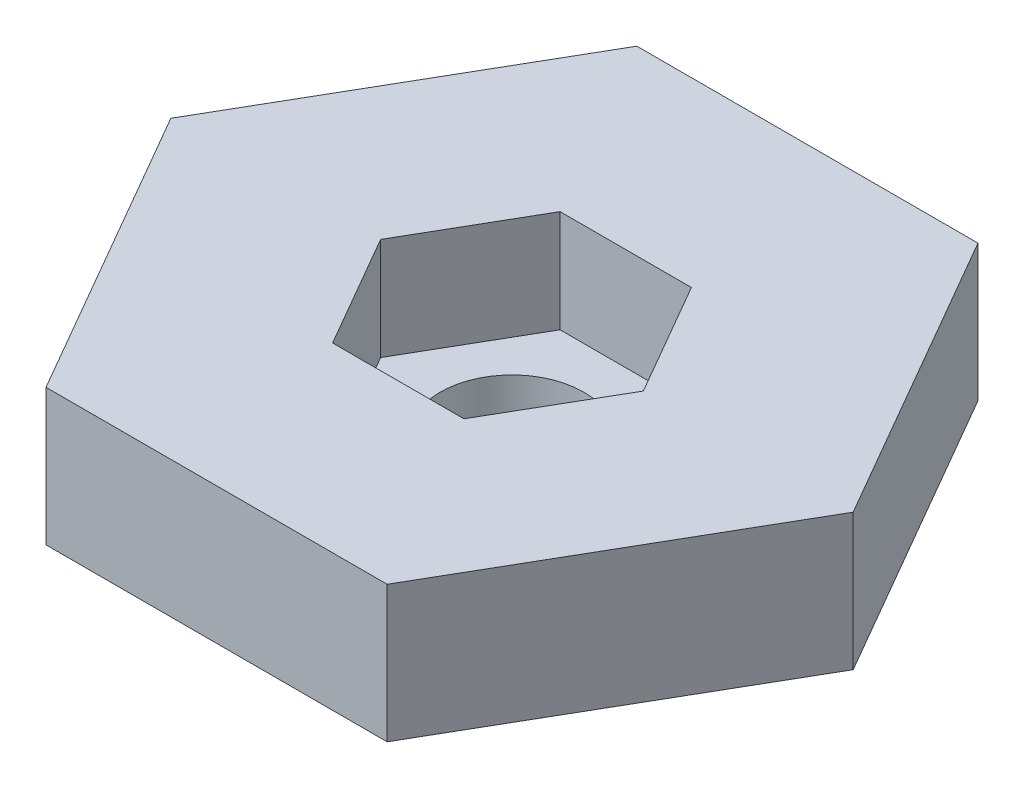
SolidWorks part; units mm, degrees
ref_plane "Спереди" through (0, 0, 0) normal (0, 0, 1) x (1, 0, 0)
ref_plane "Сверху" through (0, 0, 0) normal (0, 1, 0) x (1, 0, 0)
ref_plane "Справа" through (0, 0, 0) normal (1, 0, 0) x (0, 0, -1)
sketch "Sketch1" plane through (0, 0, 0) normal (0, 1, 0) x (1, 0, 0)
  line L1 (-10, 17.3205) -> (-20, 0)
  line L2 (-20, 0) -> (-10, -17.3205)
  line L3 (-10, -17.3205) -> (10, -17.3205)
  line L4 (10, -17.3205) -> (20, 0)
  line L5 (20, 0) -> (10, 17.3205)
  line L6 (10, 17.3205) -> (-10, 17.3205)
  line L7 (-3.85, 6.6684) -> (-7.7, 0)
  line L8 (-7.7, 0) -> (-3.85, -6.6684)
  line L9 (-3.85, -6.6684) -> (3.85, -6.6684)
  line L10 (3.85, -6.6684) -> (7.7, 0)
  line L11 (7.7, 0) -> (3.85, 6.6684)
  line L12 (3.85, 6.6684) -> (-3.85, 6.6684)
  circle A0 centre (0, 0) radius 20 construction
  circle A1 centre (0, 0) radius 7.7 construction
  dimension "D1" = 40
  dimension "D2" = 15.4
extrude "Boss-Extrude1" add sketch "Sketch1" along normal blind 6
sketch "Sketch2" plane through (0, 0, 0) normal (0, -1, 0) x (1, 0, 0)
  line L0 (20, 0) -> (10, -17.3205)
  line L1 (10, -17.3205) -> (-10, -17.3205)
  line L2 (-10, -17.3205) -> (-20, 0)
  line L3 (-20, 0) -> (-10, 17.3205)
  line L4 (-20, 0) -> (-10, 17.3205) construction
  line L5 (-10, 17.3205) -> (10, 17.3205) construction
  line L6 (-10, 17.3205) -> (10, 17.3205)
  line L7 (10, 17.3205) -> (20, 0)
  circle A0 centre (0, 0) radius 4.2
  dimension "D1" = 8.4
extrude "Boss-Extrude2" add sketch "Sketch2" along normal blind 2
